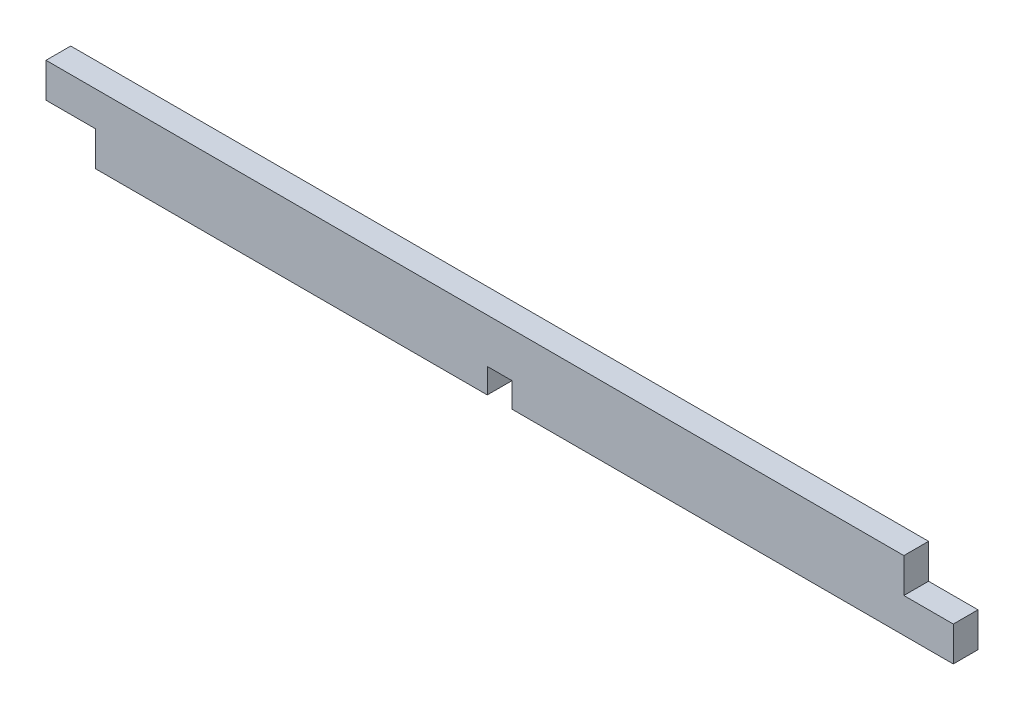
SolidWorks part; units mm, degrees
material "Сосна обыкновенная"
ref_plane "Front Plane" through (0, 0, 0) normal (0, 0, 1) x (1, 0, 0)
ref_plane "Top Plane" through (0, 0, 0) normal (0, 1, 0) x (1, 0, 0)
ref_plane "Right Plane" through (0, 0, 0) normal (1, 0, 0) x (0, 0, -1)
sketch "Эскиз1" plane through (0, 0, 0) normal (0, 0, 1) x (1, 0, 0)
  line L0 (-51.4, 0) -> (-45.8, 0)
  line L1 (-45.8, -3.92) -> (-1.4, -3.92)
  line L2 (-51.4, 0) -> (-51.4, 3.92)
  line L3 (-51.4, 3.92) -> (45.8, 3.92)
  line L4 (51.4, -3.92) -> (51.4, 0)
  line L5 (-51.4, -3.92) -> (51.4, 3.92) construction
  line L6 (-51.4, 3.92) -> (51.4, -3.92) construction
  line L7 (-45.8, 0) -> (-45.8, -3.92)
  line L8 (45.8, 3.92) -> (45.8, 0)
  line L9 (45.8, 0) -> (51.4, 0)
  line L10 (0, 3.92) -> (0, -8.4274) construction
  line L11 (1.4, -3.92) -> (51.4, -3.92)
  line L13 (-1.4, -3.92) -> (-1.4, -1.12)
  line L14 (-1.4, -1.12) -> (1.4, -1.12)
  line L15 (1.4, -3.92) -> (1.4, -1.12)
  line L16 (0, -3.92) -> (1.4, -1.12) construction
  line L17 (-1.4, -1.12) -> (0, -3.92) construction
  point P0 (0, 0)
  point P8 (0, -3.92)
  point P13 (0, -3.92)
  dimension "D1" = 7.84
  dimension "D2" = 102.8
  dimension "D3" = 5.6
  dimension "D4" = 5.6
  dimension "D5" = 2.8
  dimension "D6" = 1.4
  dimension "D7" = 2.8
extrude "Бобышка-Вытянуть1" add sketch "Эскиз1" along normal mid plane 2.8
equation "\"thickness\"= 2.8"
equation "\"a\"= 1.8"
equation "\"D1@Эскиз1\"=\"thickness\"*\"a\"+\"thickness\""
equation "\"D2@Эскиз1\"=\"thickness\"+100"
equation "\"D3@Эскиз1\"=\"thickness\"*2"
equation "\"D4@Эскиз1\"=\"thickness\"*2"
equation "\"D5@Эскиз1\"=\"thickness\""
equation "\"D6@Эскиз1\"=\"thickness\"/2"
equation "\"D7@Эскиз1\"=\"thickness\""
equation "\"D1@Бобышка-Вытянуть1\"=\"thickness\""
